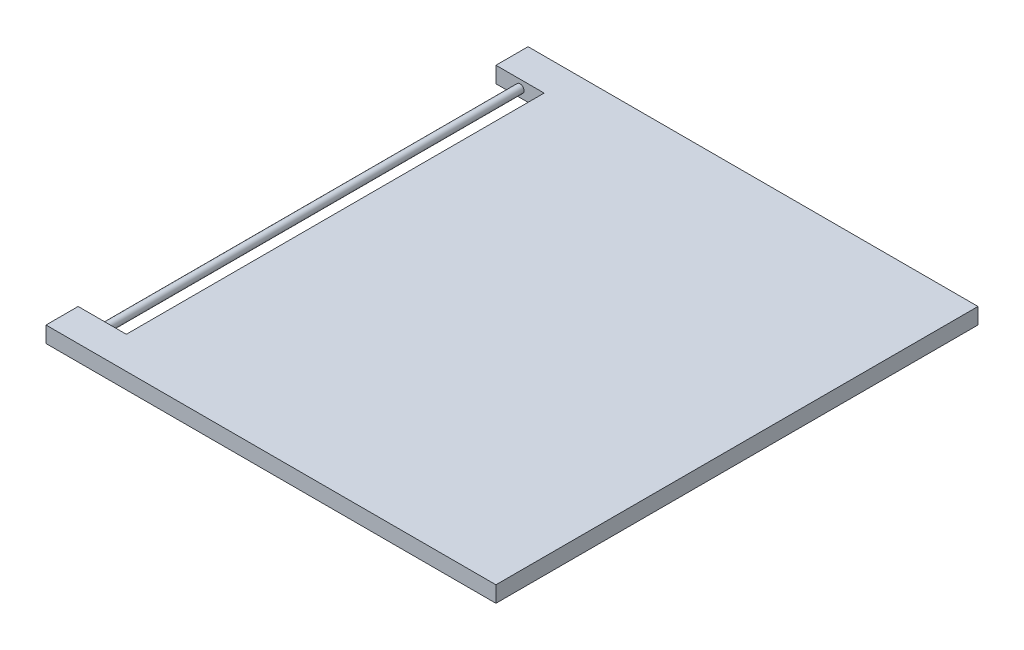
SolidWorks part; units mm, degrees
ref_plane "Front Plane" through (0, 0, 0) normal (0, 0, 1) x (1, 0, 0)
ref_plane "Top Plane" through (0, 0, 0) normal (0, 1, 0) x (1, 0, 0)
ref_plane "Right Plane" through (0, 0, 0) normal (1, 0, 0) x (0, 0, -1)
sketch "Sketch1" plane through (0, 0, 0) normal (0, 1, 0) x (1, 0, 0)
  line L1 (-108.7209, 86.9186) -> (141.2791, 86.9186)
  line L2 (-108.7209, 86.9186) -> (-108.7209, -213.0814)
  line L3 (-108.7209, -213.0814) -> (141.2791, -213.0814)
  line L4 (141.2791, 86.9186) -> (141.2791, -213.0814)
  dimension "D1" = 250
  dimension "D2" = 300
extrude "Boss-Extrude1" add sketch "Sketch1" along normal blind 10 contours L2 L1 L4 L3
sketch "Sketch2" plane through (-108.7209, 0, 0) normal (-1, 0, 0) x (0, 0, 1)
  line L0 (-86.9186, 0) -> (213.0814, 0) construction
  line L1 (-86.9186, 10) -> (-66.9186, 10)
  line L2 (-86.9186, 10) -> (-86.9186, 0)
  line L3 (-86.9186, 0) -> (-66.9186, 0)
  line L4 (-66.9186, 10) -> (-66.9186, 0)
  line L6 (213.0814, 10) -> (193.0814, 10)
  line L7 (213.0814, 10) -> (213.0814, 0)
  line L8 (213.0814, 0) -> (193.0814, 0)
  line L9 (193.0814, 10) -> (193.0814, 0)
  dimension "D1" = 20
  dimension "D2" = 20
extrude "Boss-Extrude2" add sketch "Sketch2" along normal blind 30
sketch "Sketch3" plane through (0, 0, -66.9186) normal (0, 0, 1) x (1, 0, 0)
  line L0 (-138.7209, 10) -> (-108.7209, 10) construction
  line L1 (-138.7209, 0) -> (-138.7209, 10) construction
  circle A0 centre (-123.7209, 5) radius 2.5
  dimension "D1" = 5
  dimension "D2" = 5
  dimension "D3" = 15
extrude "Boss-Extrude3" add sketch "Sketch3" along normal up to surface (260 mm away) contours A0 up to face at (-123.7209, 5, 193.0814)
